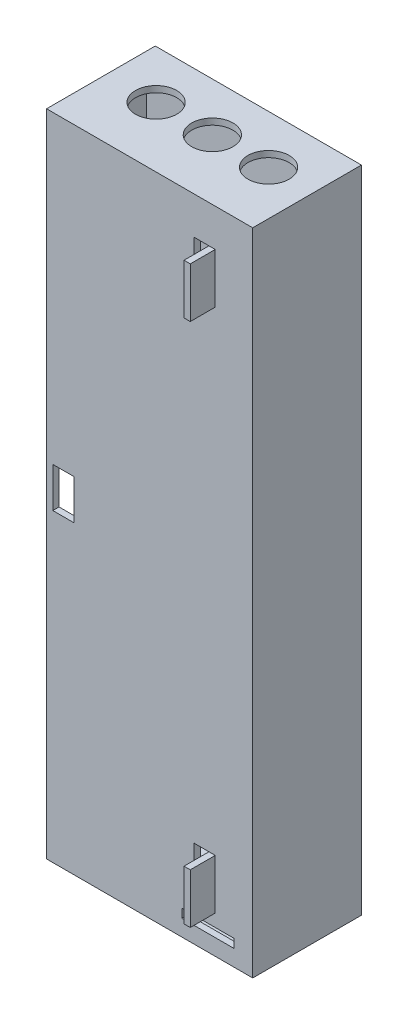
SolidWorks part; units mm, degrees
material "PLA"
ref_plane "Front Plane" through (0, 0, 0) normal (1, 0, 0) x (0, 1, 0)
ref_plane "Top Plane" through (0, 0, 0) normal (0, 0, 1) x (0, 1, 0)
ref_plane "Right Plane" through (0, 0, 0) normal (0, 1, 0) x (-1, 0, 0)
sketch "Sketch1" plane through (0, 0, 0) normal (0, 0, 1) x (0, 1, 0)
  line L1 (-130, -42.5) -> (130, -42.5)
  line L2 (-130, -42.5) -> (-130, 42.5)
  line L3 (-130, 42.5) -> (130, 42.5)
  line L4 (130, -42.5) -> (130, 42.5)
  line L5 (-130, -42.5) -> (130, 42.5) construction
  line L6 (-130, 42.5) -> (130, -42.5) construction
  point P0 (0, 0)
  dimension "D1" = 260
extrude "Boss-Extrude1" add sketch "Sketch1" along normal blind 2.5
sketch "Sketch2" plane through (0, 0, 0) normal (0, 0, -1) x (1, 0, 0)
  line L1 (-42.5, 130) -> (42.5, 130) construction
  line L2 (-40, -127.5) -> (40, -127.5)
  line L3 (-40, -127.5) -> (-40, 127.5)
  line L4 (-42.5, -130) -> (42.5, -130)
  line L5 (42.5, -130) -> (42.5, 130)
  line L6 (42.5, 130) -> (-42.5, 130)
  line L7 (-42.5, 130) -> (-42.5, -130)
  line L8 (-42.5, -130) -> (42.5, -130)
  line L9 (42.5, -130) -> (42.5, 130)
  line L10 (42.5, 130) -> (-42.5, 130)
  line L11 (-42.5, 130) -> (-42.5, -130)
  line L12 (-40, 127.5) -> (40, 127.5)
  line L13 (40, -127.5) -> (40, 127.5)
  line L14 (-40, -127.5) -> (40, 127.5) construction
  line L15 (-40, 127.5) -> (40, -127.5) construction
  point P2 (0, 0)
  dimension "D2" = 2.5
  dimension "D3" = 2.5
extrude "Boss-Extrude2" add sketch "Sketch2" along normal blind 35
sketch "Sketch3" plane through (0, 0, -35) normal (0, 0, -1) x (1, 0, 0)
  line L1 (42.5, 130) -> (-42.5, 130)
  line L2 (42.5, 130) -> (42.5, -130)
  line L3 (42.5, -130) -> (-42.5, -130)
  line L4 (-42.5, 130) -> (-42.5, -130)
extrude "Boss-Extrude3" add sketch "Sketch3" along normal blind 6
sketch "Sketch4" plane through (-42.5, 0, 0) normal (-1, 0, 0) x (0, -1, 0)
  line L5 (-130, 2.5) -> (130, 2.5)
  line L6 (-130, 2.5) -> (-130, -41)
  line L7 (-130, -41) -> (130, -41)
  line L8 (130, 2.5) -> (130, -41)
extrude "Cut-Extrude1" cut sketch "Sketch4" against normal blind 2.5
sketch "Sketch5" plane through (0, 0, 2.5) normal (0, 0, 1) x (1, 0, 0)
  line L0 (-29, 0) -> (-37.5, 0) construction
  line L1 (-37.5, 8) -> (-29, 8)
  line L2 (-37.5, 8) -> (-37.5, -8)
  line L3 (-37.5, -8) -> (-29, -8)
  line L4 (-29, 8) -> (-29, -8)
  line L6 (0, 0) -> (-40, 0) construction
  line L7 (-40, -130) -> (-40, 130) construction
  dimension "D3" = 2.5
  dimension "D1" = 16
  dimension "D2" = 8.5
extrude "Cut-Extrude2" cut sketch "Sketch5" against normal up to next
sketch "Sketch14" plane through (0, -130, 0) normal (0, -1, 0) x (1, 0, 0)
  circle A0 centre (-20.9549, -21.3351) radius 7.42 construction
  circle A1 centre (-20.9549, -21.3351) radius 7.42 construction
  circle A2 centre (-20.9549, -21.3351) radius 8.25
  dimension "D1" = 16.5
extrude "Cut-Extrude8" cut sketch "Sketch14" against normal up to surface (2.5 mm away) up to face at (0, -127.5, -17.5)
sketch "Sketch21" plane through (0, 0, -41) normal (0, 0, -1) x (-1, 0, 0)
  line L8 (-42.5, -130) -> (40, -130)
  line L9 (40, -130) -> (40, 130)
  line L10 (40, 130) -> (-42.5, 130)
  line L11 (-42.5, 130) -> (-42.5, -130)
  line L12 (-42.5, -130) -> (40, -130)
  line L13 (40, -130) -> (40, 130)
  line L14 (40, 130) -> (-42.5, 130)
  line L15 (-42.5, 130) -> (-42.5, -130)
  line L16 (-24.35, 12.9) -> (5.65, 12.9) construction
  line L17 (5.65, 17.1) -> (-24.35, 17.1) construction
  line L18 (-24.35, 12.9) -> (5.65, 12.9) construction
  line L19 (5.65, 17.1) -> (-24.35, 17.1) construction
  line L20 (-9.35, 17.1) -> (-9.35, 12.9) construction
  line L24 (3.15, 15) -> (-21.85, 15) construction
  arc A0 (5.65, 12.9) -> (7.75, 15) centre (5.65, 15) ccw construction
  arc A1 (7.75, 15) -> (5.65, 17.1) centre (5.65, 15) ccw construction
  arc A2 (-26.45, 15) -> (-24.35, 12.9) centre (-24.35, 15) ccw construction
  arc A3 (-24.35, 17.1) -> (-26.45, 15) centre (-24.35, 15) ccw construction
  arc A4 (5.65, 12.9) -> (7.75, 15) centre (5.65, 15) ccw construction
  arc A5 (7.75, 15) -> (5.65, 17.1) centre (5.65, 15) ccw construction
  arc A6 (-26.45, 15) -> (-24.35, 12.9) centre (-24.35, 15) ccw construction
  arc A7 (-24.35, 17.1) -> (-26.45, 15) centre (-24.35, 15) ccw construction
  point P47 (-21.85, 15)
  point P270 (3.15, 15)
  point P271 (-9.35, 15)
  point P283 (-21.85, 15)
  point P285 (3.15, 15)
  dimension "D2" = 25
  dimension "D1" = 0
hole_wizard "CBORE for M4 Hex Head Machine Screw1" [suppressed] positions "Sketch21" profile "Sketch20" counterbore size "M4" standard "ANSI Metric"
sketch "Sketch20" plane through (33.829, -125, -41) normal (1, 0, 0) x (0, 1, 0)
  line L0 (0, 0) -> (0, 7.3519)
  line L1 (0, 7.3519) -> (2.25, 6)
  line L2 (2.25, 6) -> (2.25, 4)
  line L3 (2.25, 4) -> (5.295, 4)
  line L4 (5.295, 4) -> (5.295, 0)
  line L5 (5.295, 0) -> (0, 0)
  line L10 (0, 7.3519) -> (-2.25, 6) construction
  line L11 (0, -6.35) -> (0, 107.95) construction
  dimension "Hole Dia." = 4.5
  dimension "Hole Depth" = 6
  dimension "C'Bore Dia." = 10.59
  dimension "C'Bore Depth" = 4
  dimension "Drill Angle" = 118
mirror "Mirror1" [suppressed] about plane through (0, 0, 0) normal (0, 1, 0)
sketch "Sketch22" plane through (0, 130, 0) normal (0, 1, 0) x (-1, 0, 0)
  circle A0 centre (20.2971, -21.6344) radius 7.42 construction
  circle A1 centre (-2.2029, -21.6344) radius 7.42 construction
  circle A2 centre (-24.7029, -21.6344) radius 7.42 construction
  circle A3 centre (20.2971, -21.6344) radius 7.42 construction
  circle A4 centre (-2.2029, -21.6344) radius 7.42 construction
  circle A5 centre (-24.7029, -21.6344) radius 7.42 construction
  circle A6 centre (-24.7029, -21.6344) radius 8.25
  circle A7 centre (-2.2029, -21.6344) radius 8.25
  circle A8 centre (20.2971, -21.6344) radius 8.25
  dimension "D1" = 16.5
extrude "Cut-Extrude9" cut sketch "Sketch22" against normal blind 10
sketch "Sketch25" plane through (0, 0, 2.5) normal (0, 0, 1) x (1, 0, 0)
  line L0 (40, 127.5) -> (40, -127.5) construction
  line L7 (14.1153, -123.5) -> (35, -123.5)
  line L8 (14.1153, -123.5) -> (14.1153, -120)
  line L9 (14.1153, -120) -> (35, -120)
  line L10 (35, -123.5) -> (35, -120)
  line L11 (14.1153, -123.5) -> (35, -120) construction
  line L12 (14.1153, -120) -> (35, -123.5) construction
  line L13 (-40, -130) -> (42.5, -130) construction
  point P5 (24.5577, -121.75)
  dimension "D1" = 5
  dimension "D2" = 20.8847
  dimension "D3" = 3.5
  dimension "D4" = 6.5
extrude "Cut-Extrude11" cut sketch "Sketch25" against normal up to next
sketch "Sketch27" plane through (-40, 0, 0) normal (-1, 0, 0) x (0, -1, 0)
  line L0 (-130, -41) -> (130, -41) construction
  line L1 (-130, 2.5) -> (-100, 2.5)
  line L2 (-130, 2.5) -> (-130, -41)
  line L3 (-130, -41) -> (-100, -41)
  line L4 (-100, 2.5) -> (-100, -41)
  line L6 (130, 2.5) -> (100, 2.5)
  line L7 (130, 2.5) -> (130, -41)
  line L8 (130, -41) -> (100, -41)
  line L9 (100, 2.5) -> (100, -41)
  dimension "D1" = 30
  dimension "D2" = 30
extrude "Boss-Extrude4" add sketch "Sketch27" against normal blind 2.5
sketch "Sketch29" plane through (0, 0, 2.5) normal (0, 0, 1) x (1, 0, 0)
  line L0 (42.5, -130) -> (42.5, 130) construction
  line L1 (25, -95) -> (27.5, -95)
  line L2 (25, -95) -> (25, -115)
  line L3 (25, -115) -> (27.5, -115)
  line L4 (27.5, -95) -> (27.5, -115)
  line L5 (-40, -130) -> (42.5, -130) construction
  dimension "D1" = 20
  dimension "D2" = 2.5
  dimension "D3" = 15
  dimension "D4" = 15
extrude "Boss-Extrude5" add sketch "Sketch29" along normal blind 10
sketch "Sketch30" plane through (0, 0, 2.5) normal (0, 0, 1) x (1, 0, 0)
  line L0 (25, -115) -> (27.5, -115) construction
  line L1 (25, -95) -> (19, -95)
  line L2 (25, -95) -> (25, -115)
  line L3 (25, -115) -> (19, -115)
  line L4 (19, -95) -> (19, -115)
  dimension "D1" = 6
extrude "Cut-Extrude12" cut sketch "Sketch30" against normal blind 5
mirror "Mirror2" about plane through (0, 0, 0) normal (0, 1, 0) of "Cut-Extrude12", "Boss-Extrude5"
equation "\"ball_diameter\"= 0.75in"
equation "\"wall_thickness\" = 0.25cm"
equation "\"track_length\" = 25cm"
equation "\"axle\" = 5mm"
equation "\"D1@Sketch1\"=\"track_length\" +1"
equation "\"D1@Boss-Extrude1\"=\"wall_thickness\""
equation "\"D2@Sketch2\"=\"wall_thickness\""
equation "\"D3@Sketch2\"=\"wall_thickness\""
equation "\"D1@Boss-Extrude3\"=0.60"
equation "\"D3@Sketch5\"=\"wall_thickness\""
